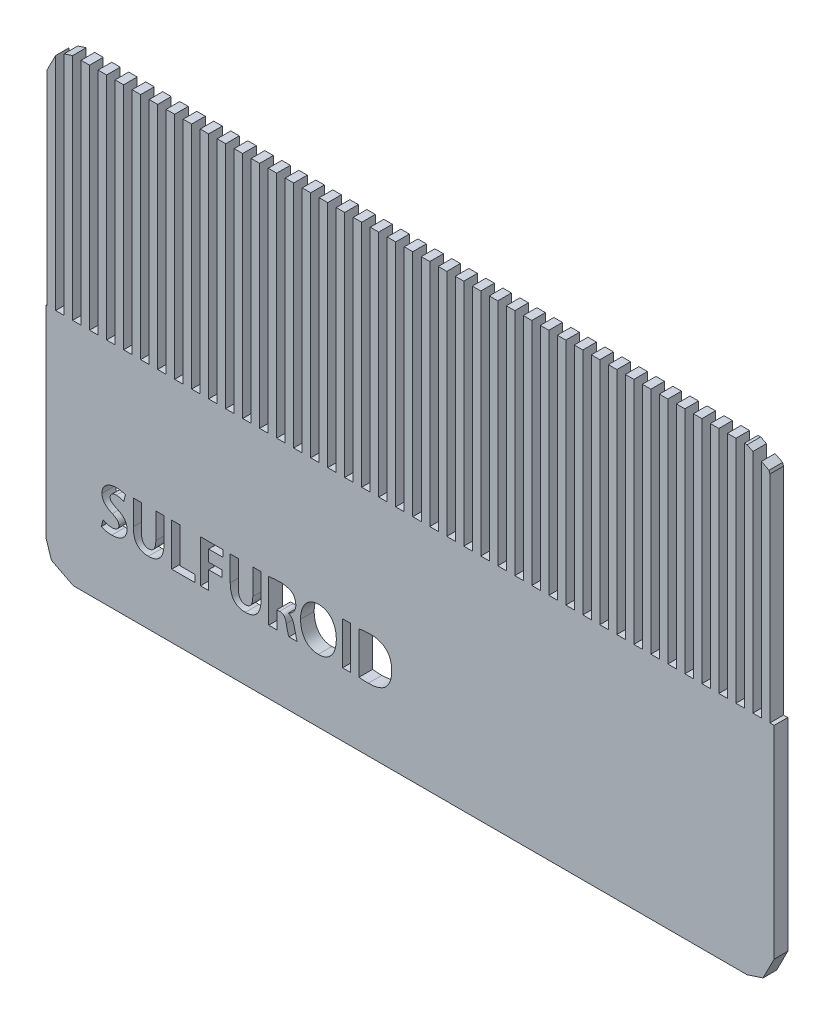
SolidWorks part; units mm, degrees
material "Plastique personnalisé"
ref_plane "Plan de face" through (0, 0, 0) normal (0, 0, 1) x (1, 0, 0)
ref_plane "Plan de dessus" through (0, 0, 0) normal (0, 1, 0) x (1, 0, 0)
ref_plane "Plan de droite" through (0, 0, 0) normal (1, 0, 0) x (0, 0, -1)
sketch "Model" plane through (0, 0, 0) normal (0, 0, 1) x (1, 0, 0)
  line L0 (39.3, 0) -> (38.3, 0)
  line L1 (38.3, 0) -> (38.3, 26.99)
  line L2 (38.3, 26.99) -> (37.3, 26.99)
  line L3 (37.3, 26.99) -> (37.3, 0)
  line L4 (37.3, 0) -> (36.3, 0)
  line L5 (36.3, 0) -> (36.3, 26.99)
  line L6 (36.3, 26.99) -> (35.3, 26.99)
  line L7 (35.3, 26.99) -> (35.3, 0)
  line L8 (35.3, 0) -> (34.3, 0)
  line L9 (34.3, 0) -> (34.3, 26.99)
  line L10 (34.3, 26.99) -> (33.3, 26.99)
  line L11 (33.3, 26.99) -> (33.3, 0)
  line L12 (33.3, 0) -> (32.3, 0)
  line L13 (32.3, 0) -> (32.3, 26.99)
  line L14 (32.3, 26.99) -> (31.3, 26.99)
  line L15 (31.3, 26.99) -> (31.3, 0)
  line L16 (31.3, 0) -> (30.3, 0)
  line L17 (30.3, 0) -> (30.3, 26.99)
  line L18 (30.3, 26.99) -> (29.3, 26.99)
  line L19 (29.3, 26.99) -> (29.3, 0)
  line L20 (29.3, 0) -> (28.3, 0)
  line L21 (28.3, 0) -> (28.3, 26.99)
  line L22 (28.3, 26.99) -> (27.3, 26.99)
  line L23 (27.3, 26.99) -> (27.3, 0)
  line L24 (27.3, 0) -> (26.3, 0)
  line L25 (26.3, 0) -> (26.3, 26.99)
  line L26 (26.3, 26.99) -> (25.3, 26.99)
  line L27 (25.3, 26.99) -> (25.3, 0)
  line L28 (25.3, 0) -> (24.3, 0)
  line L29 (24.3, 0) -> (24.3, 26.99)
  line L30 (24.3, 26.99) -> (23.3, 26.99)
  line L31 (23.3, 26.99) -> (23.3, 0)
  line L32 (23.3, 0) -> (22.3, 0)
  line L33 (22.3, 0) -> (22.3, 26.99)
  line L34 (22.3, 26.99) -> (21.3, 26.99)
  line L35 (21.3, 26.99) -> (21.3, 0)
  line L36 (21.3, 0) -> (20.3, 0)
  line L37 (20.3, 0) -> (20.3, 26.99)
  line L38 (20.3, 26.99) -> (19.3, 26.99)
  line L39 (19.3, 26.99) -> (19.3, 0)
  line L40 (19.3, 0) -> (18.3, 0)
  line L41 (18.3, 0) -> (18.3, 26.99)
  line L42 (18.3, 26.99) -> (17.3, 26.99)
  line L43 (17.3, 26.99) -> (17.3, 0)
  line L44 (17.3, 0) -> (16.3, 0)
  line L45 (16.3, 0) -> (16.3, 26.99)
  line L46 (16.3, 26.99) -> (15.3, 26.99)
  line L47 (15.3, 26.99) -> (15.3, 0)
  line L48 (15.3, 0) -> (14.3, 0)
  line L49 (14.3, 0) -> (14.3, 26.99)
  line L50 (14.3, 26.99) -> (13.3, 26.99)
  line L51 (13.3, 26.99) -> (13.3, 0)
  line L52 (13.3, 0) -> (12.3, 0)
  line L53 (12.3, 0) -> (12.3, 26.99)
  line L54 (12.3, 26.99) -> (11.3, 26.99)
  line L55 (11.3, 26.99) -> (11.3, 0)
  line L56 (11.3, 0) -> (10.3, 0)
  line L57 (10.3, 0) -> (10.3, 26.99)
  line L58 (10.3, 26.99) -> (9.3, 26.99)
  line L59 (9.3, 26.99) -> (9.3, 0)
  line L60 (9.3, 0) -> (8.3, 0)
  line L61 (8.3, 0) -> (8.3, 26.99)
  line L62 (8.3, 26.99) -> (7.3, 26.99)
  line L63 (7.3, 26.99) -> (7.3, 0)
  line L64 (7.3, 0) -> (6.3, 0)
  line L65 (6.3, 0) -> (6.3, 26.99)
  line L66 (6.3, 26.99) -> (5.3, 26.99)
  line L67 (5.3, 26.99) -> (5.3, 0)
  line L68 (5.3, 0) -> (4.3, 0)
  line L69 (4.3, 0) -> (4.3, 26.99)
  line L70 (4.3, 26.99) -> (3.3, 26.99)
  line L71 (3.3, 26.99) -> (3.3, 0)
  line L72 (3.3, 0) -> (2.3, 0)
  line L73 (2.3, 0) -> (2.3, 26.99)
  line L74 (2.3, 26.99) -> (1.3, 26.99)
  line L75 (1.3, 26.99) -> (1.3, 0)
  line L76 (1.3, 0) -> (0.3, 0)
  line L77 (0.3, 0) -> (0.3, 26.99)
  line L78 (0.3, 26.99) -> (-0.7, 26.99)
  line L79 (-0.7, 26.99) -> (-0.7, 0)
  line L80 (-0.7, 0) -> (-1.7, 0)
  line L81 (-1.7, 0) -> (-1.7, 26.99)
  line L82 (-1.7, 26.99) -> (-2.7, 26.99)
  line L83 (-2.7, 26.99) -> (-2.7, 0)
  line L84 (-2.7, 0) -> (-3.7, 0)
  line L85 (-3.7, 0) -> (-3.7, 26.99)
  line L86 (-3.7, 26.99) -> (-4.7, 26.99)
  line L87 (-4.7, 26.99) -> (-4.7, 0)
  line L88 (-4.7, 0) -> (-5.7, 0)
  line L89 (-5.7, 0) -> (-5.7, 26.99)
  line L90 (-5.7, 26.99) -> (-6.7, 26.99)
  line L91 (-6.7, 26.99) -> (-6.7, 0)
  line L92 (-6.7, 0) -> (-7.7, 0)
  line L93 (-7.7, 0) -> (-7.7, 26.99)
  line L94 (-7.7, 26.99) -> (-8.7, 26.99)
  line L95 (-8.7, 26.99) -> (-8.7, 0)
  line L96 (-8.7, 0) -> (-9.7, 0)
  line L97 (-9.7, 0) -> (-9.7, 26.99)
  line L98 (-9.7, 26.99) -> (-10.7, 26.99)
  line L99 (-10.7, 26.99) -> (-10.7, 0)
  line L100 (-10.7, 0) -> (-11.7, 0)
  line L101 (-11.7, 0) -> (-11.7, 26.99)
  line L102 (-11.7, 26.99) -> (-12.7, 26.99)
  line L103 (-12.7, 26.99) -> (-12.7, 0)
  line L104 (-12.7, 0) -> (-13.7, 0)
  line L105 (-13.7, 0) -> (-13.7, 26.99)
  line L106 (-13.7, 26.99) -> (-14.7, 26.99)
  line L107 (-14.7, 26.99) -> (-14.7, 0)
  line L108 (-14.7, 0) -> (-15.7, 0)
  line L109 (-15.7, 0) -> (-15.7, 26.99)
  line L110 (-15.7, 26.99) -> (-16.7, 26.99)
  line L111 (-16.7, 26.99) -> (-16.7, 0)
  line L112 (-16.7, 0) -> (-17.7, 0)
  line L113 (-17.7, 0) -> (-17.7, 26.99)
  line L114 (-17.7, 26.99) -> (-18.7, 26.99)
  line L115 (-18.7, 26.99) -> (-18.7, 0)
  line L116 (-18.7, 0) -> (-19.7, 0)
  line L117 (-19.7, 0) -> (-19.7, 26.99)
  line L118 (-19.7, 26.99) -> (-20.7, 26.99)
  line L119 (-20.7, 26.99) -> (-20.7, 0)
  line L120 (-20.7, 0) -> (-21.7, 0)
  line L121 (-21.7, 0) -> (-21.7, 26.99)
  line L122 (-21.7, 26.99) -> (-22.7, 26.99)
  line L123 (-22.7, 26.99) -> (-22.7, 0)
  line L124 (-22.7, 0) -> (-23.7, 0)
  line L125 (-23.7, 0) -> (-23.7, 26.99)
  line L126 (-23.7, 26.99) -> (-24.7, 26.99)
  line L127 (-24.7, 26.99) -> (-24.7, 0)
  line L128 (-24.7, 0) -> (-25.7, 0)
  line L129 (-25.7, 0) -> (-25.7, 26.99)
  line L130 (-25.7, 26.99) -> (-26.7, 26.99)
  line L131 (-26.7, 26.99) -> (-26.7, 0)
  line L132 (-26.7, 0) -> (-27.7, 0)
  line L133 (-27.7, 0) -> (-27.7, 26.99)
  line L134 (-27.7, 26.99) -> (-28.7, 26.99)
  line L135 (-28.7, 26.99) -> (-28.7, 0)
  line L136 (-28.7, 0) -> (-29.7, 0)
  line L137 (-29.7, 0) -> (-29.7, 26.99)
  line L138 (-29.7, 26.99) -> (-30.7, 26.99)
  line L139 (-30.7, 26.99) -> (-30.7, 0)
  line L140 (-30.7, 0) -> (-31.7, 0)
  line L141 (-31.7, 0) -> (-31.7, 26.99)
  line L142 (-31.7, 26.99) -> (-32.7, 26.99)
  line L143 (-32.7, 26.99) -> (-32.7, 0)
  line L144 (-32.7, 0) -> (-33.7, 0)
  line L145 (-33.7, 0) -> (-33.7, 26.99)
  line L146 (-33.7, 26.99) -> (-34.7, 26.99)
  line L147 (-34.7, 26.99) -> (-34.7, 0)
  line L148 (-34.7, 0) -> (-35.7, 0)
  line L149 (-35.7, 0) -> (-35.7, 26.99)
  line L150 (-35.7, 26.99) -> (-36.7, 26.99)
  line L151 (-36.7, 26.99) -> (-36.7, 0)
  line L152 (-36.7, 0) -> (-37.7, 0)
  line L153 (-37.7, 0) -> (-37.7, 26.99)
  line L154 (-37.7, 26.99) -> (-38.7, 26.99)
  line L155 (-38.7, 26.99) -> (-38.7, 0)
  line L156 (-38.7, 0) -> (-39.7, 0)
  line L157 (-39.7, 0) -> (-39.7, 26.964)
  line L158 (-39.7, 26.964) -> (-40.7, 26.6391)
  line L159 (-40.7, 26.6391) -> (-40.7, 0)
  line L160 (-40.7, 0) -> (-41.7, 0)
  line L161 (-41.7, 0) -> (-41.7, 25.9689)
  line L162 (-41.7, 25.9689) -> (-42.7, 24.0062)
  line L163 (-42.7, 24.0062) -> (-42.7, 0)
  line L164 (-42.7, 0) -> (-42.8, 0)
  line L165 (-42.8, 0) -> (-42.8, -23.81)
  line L166 (-42.8, -23.81) -> (-42.1927, -25.6792)
  line L167 (-42.1927, -25.6792) -> (-39.62, -26.99)
  line L168 (-39.62, -26.99) -> (39.62, -26.99)
  line L169 (39.62, -26.99) -> (41.4892, -26.3827)
  line L170 (41.4892, -26.3827) -> (42.8, -23.81)
  line L171 (42.8, -23.81) -> (42.8, 0)
  line L172 (42.8, 0) -> (42.3, 0)
  line L173 (42.3, 0) -> (42.3, 25.3489)
  line L174 (42.3, 25.3489) -> (42.1927, 25.6792)
  line L175 (42.1927, 25.6792) -> (41.3, 26.134)
  line L176 (41.3, 26.134) -> (41.3, 0)
  line L177 (41.3, 0) -> (40.3, 0)
  line L178 (40.3, 0) -> (40.3, 26.6435)
  line L179 (40.3, 26.6435) -> (39.62, 26.99)
  line L180 (39.62, 26.99) -> (39.3, 26.99)
  line L181 (39.3, 26.99) -> (39.3, 0)
extrude "Boss.-Extru.1" add sketch "Model" along normal blind 1.6 contours L180 L181 L0 L1 L2 L3 L4 L5 L6 L7 L8 L9 L10 L11 L12 L13 L14 L15 L16 L17 L18 L19 L20 L21 L22 L23 L24 L25 L26 L27 L28 L29 L30 L31 L32 L33 L34 L35 L36 L37 L38 L39 L40 L41 L42 L43 L44 L45 L46 L47 L48
sketch "Esquisse2" plane through (0, 0, 1.6) normal (0, 0, 1) x (1, 0, 0)
  text T0 "SULFUROID" font "Adobe Gothic Std B" height 5
extrude "Enlèv. mat.-Extru.1" cut sketch "Esquisse2" against normal blind 1.6
sketch "Esquisse3" plane through (0, 0, 1.6) normal (0, 0, 1) x (1, 0, 0)
  line L1 (-16.0811, -16.8917) -> (-14.2111, -16.8917)
  line L2 (-16.0811, -16.8917) -> (-16.0811, -15.0559)
  line L3 (-16.0811, -15.0559) -> (-14.2111, -15.0559)
  line L4 (-14.2111, -16.8917) -> (-14.2111, -15.0559)
  line L5 (-16.0811, -16.8917) -> (-14.2111, -15.0559) construction
  line L6 (-16.0811, -15.0559) -> (-14.2111, -16.8917) construction
  line L7 (-11.9153, -18.9123) -> (-9.6134, -18.9123)
  line L8 (-11.9153, -18.9123) -> (-11.9153, -14.8712)
  line L9 (-11.9153, -14.8712) -> (-9.6134, -14.8712)
  line L10 (-9.6134, -18.9123) -> (-9.6134, -14.8712)
  line L11 (-11.9153, -18.9123) -> (-9.6134, -14.8712) construction
  line L12 (-11.9153, -14.8712) -> (-9.6134, -18.9123) construction
  point P0 (-15.1461, -15.9738)
  point P5 (-10.7643, -16.8917)
extrude "Enlèv. mat.-Extru.2" cut sketch "Esquisse3" against normal blind 1.6
sketch "Esquisse4" plane through (0, 0, 1.6) normal (0, 0, 1) x (1, 0, 0)
  line L1 (-5.6843, -19.053) -> (-3.1259, -19.053)
  line L2 (-5.6843, -19.053) -> (-5.6843, -15.0964)
  line L3 (-5.6843, -15.0964) -> (-3.1259, -15.0964)
  line L4 (-3.1259, -19.053) -> (-3.1259, -15.0964)
  line L5 (-5.6843, -19.053) -> (-3.1259, -15.0964) construction
  line L6 (-5.6843, -15.0964) -> (-3.1259, -19.053) construction
  point P0 (-4.4051, -17.0747)
extrude "Enlèv. mat.-Extru.3" cut sketch "Esquisse4" against normal blind 1.6
